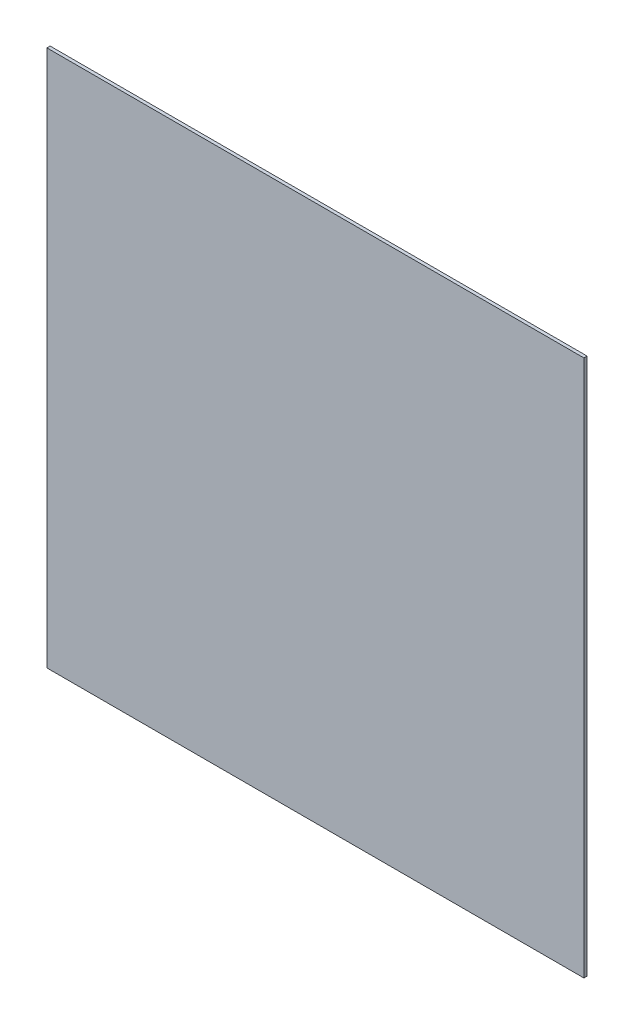
SolidWorks part; units mm, degrees
material "Acrílico (médio-alto impacto)"
ref_plane "Plano frontal" through (0, 0, 0) normal (0, 0, 1) x (1, 0, 0)
ref_plane "Plano superior" through (0, 0, 0) normal (0, 1, 0) x (1, 0, 0)
ref_plane "Plano direito" through (0, 0, 0) normal (1, 0, 0) x (0, 0, -1)
sketch "Esboço1" plane through (0, 0, 0) normal (0, 0, 1) x (1, 0, 0)
  line L1 (-500, 500) -> (500, 500)
  line L2 (-500, 500) -> (-500, -500)
  line L3 (-500, -500) -> (500, -500)
  line L4 (500, 500) -> (500, -500)
  line L5 (-500, 500) -> (500, -500) construction
  line L6 (-500, -500) -> (500, 500) construction
  point P0 (0, 0)
  dimension "D1" = 1000
  dimension "D2" = 1000
extrude "Ressalto-extrusão1" add sketch "Esboço1" along normal mid plane 6
